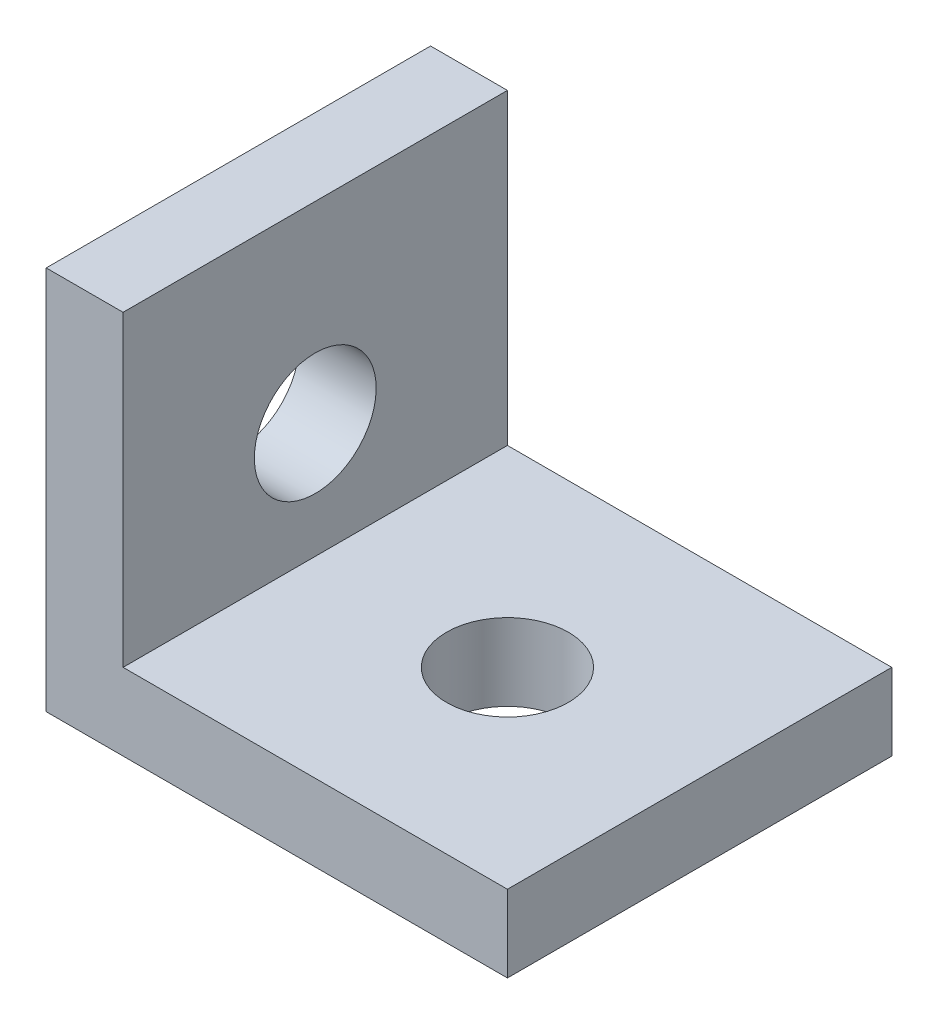
SolidWorks part; units mm, degrees
ref_plane "Front Plane" through (0, 0, 0) normal (0, 0, 1) x (1, 0, 0)
ref_plane "Top Plane" through (0, 0, 0) normal (0, 1, 0) x (1, 0, 0)
ref_plane "Right Plane" through (0, 0, 0) normal (1, 0, 0) x (0, 0, -1)
sketch "Sketch1" plane through (0, 0, 0) normal (0, 0, 1) x (1, 0, 0)
  line L1 (0, 0) -> (12, 0)
  line L2 (0, 0) -> (0, 10)
  line L3 (0, 10) -> (2, 10)
  line L4 (12, 0) -> (12, 2)
  line L7 (12, 2) -> (2, 2)
  line L8 (2, 10) -> (2, 2)
  dimension "D1" = 12
  dimension "D2" = 10
  dimension "D3" = 2
  dimension "D4" = 2
extrude "Boss-Extrude1" add sketch "Sketch1" along normal blind 10
sketch "Sketch2" plane through (0, 2, 0) normal (0, 1, 0) x (1, 0, 0)
  line L0 (2, -10) -> (12, 0) construction
  circle A0 centre (7, -5) radius 1.585
  dimension "D1" = 3.17
extrude "Cut-Extrude1" cut sketch "Sketch2" against normal through all
sketch "Sketch3" plane through (2, 0, 0) normal (1, 0, 0) x (0, 0, -1)
  line L0 (-10, 0) -> (0, 10) construction
  circle A0 centre (-5, 5) radius 1.585
  dimension "D1" = 3.17
extrude "Cut-Extrude2" cut sketch "Sketch3" against normal through all
